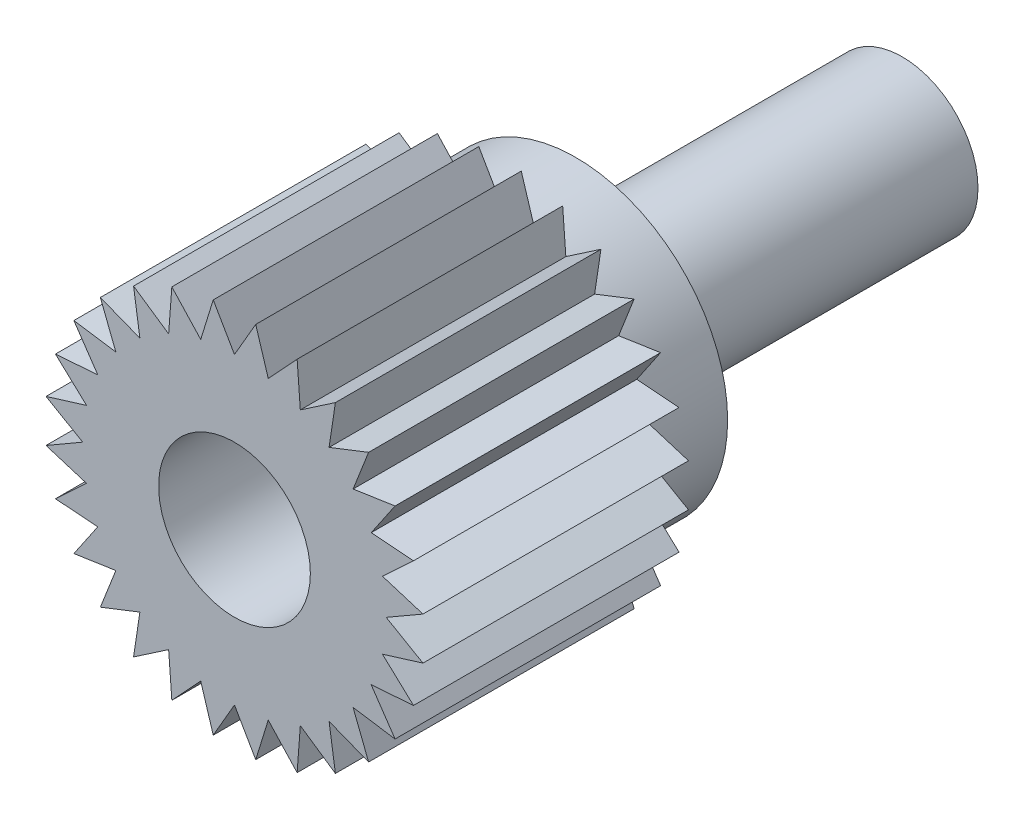
SolidWorks part; units mm, degrees
ref_plane "前视基准面" through (0, 0, 0) normal (0, 0, 1) x (1, 0, 0)
ref_plane "上视基准面" through (0, 0, 0) normal (0, 1, 0) x (1, 0, 0)
ref_plane "右视基准面" through (0, 0, 0) normal (1, 0, 0) x (0, 0, -1)
sketch "草图1" plane through (0, 0, 0) normal (0, 0, 1) x (1, 0, 0)
  circle A0 centre (0, 0) radius 1
extrude "凸台-拉伸1" add sketch "草图1" against normal blind 4.3
sketch "草图2" plane through (0, 0, 0) normal (0, 0, 1) x (1, 0, 0)
  circle A0 centre (0, 0) radius 2
extrude "凸台-拉伸2" add sketch "草图2" along normal blind 1
sketch "草图3" plane through (0, 0, 1) normal (0, 0, 1) x (1, 0, 0)
  line L0 (2.3597, -0.8257) -> (1.8019, -0.8678)
  line L29 (2.4843, -0.2799) -> (1.9499, -0.445)
  line L30 (2.4843, -0.2799) -> (2, 0)
  line L31 (2.3597, -0.8257) -> (1.9499, -0.445)
  line L32 (2.1168, -1.3301) -> (1.5637, -1.247)
  line L33 (2.1168, -1.3301) -> (1.8019, -0.8678)
  line L34 (1.7678, -1.7678) -> (1.247, -1.5637)
  line L35 (1.7678, -1.7678) -> (1.5637, -1.247)
  line L36 (1.3301, -2.1168) -> (0.8678, -1.8019)
  line L37 (1.3301, -2.1168) -> (1.247, -1.5637)
  line L38 (0.8257, -2.3597) -> (0.445, -1.9499)
  line L39 (0.8257, -2.3597) -> (0.8678, -1.8019)
  line L40 (0.2799, -2.4843) -> (0, -2)
  line L41 (0.2799, -2.4843) -> (0.445, -1.9499)
  line L42 (-0.2799, -2.4843) -> (-0.445, -1.9499)
  line L43 (-0.2799, -2.4843) -> (0, -2)
  line L44 (-0.8257, -2.3597) -> (-0.8678, -1.8019)
  line L45 (-0.8257, -2.3597) -> (-0.445, -1.9499)
  line L46 (-1.3301, -2.1168) -> (-1.247, -1.5637)
  line L47 (-1.3301, -2.1168) -> (-0.8678, -1.8019)
  line L48 (-1.7678, -1.7678) -> (-1.5637, -1.247)
  line L49 (-1.7678, -1.7678) -> (-1.247, -1.5637)
  line L50 (-2.1168, -1.3301) -> (-1.8019, -0.8678)
  line L51 (-2.1168, -1.3301) -> (-1.5637, -1.247)
  line L52 (-2.3597, -0.8257) -> (-1.9499, -0.445)
  line L53 (-2.3597, -0.8257) -> (-1.8019, -0.8678)
  line L54 (-2.4843, -0.2799) -> (-2, 0)
  line L55 (-2.4843, -0.2799) -> (-1.9499, -0.445)
  line L56 (-2.4843, 0.2799) -> (-1.9499, 0.445)
  line L57 (-2.4843, 0.2799) -> (-2, 0)
  line L58 (-2.3597, 0.8257) -> (-1.8019, 0.8678)
  line L59 (-2.3597, 0.8257) -> (-1.9499, 0.445)
  line L60 (-2.1168, 1.3301) -> (-1.5637, 1.247)
  line L61 (-2.1168, 1.3301) -> (-1.8019, 0.8678)
  line L62 (-1.7678, 1.7678) -> (-1.247, 1.5637)
  line L63 (-1.7678, 1.7678) -> (-1.5637, 1.247)
  line L64 (-1.3301, 2.1168) -> (-0.8678, 1.8019)
  line L65 (-1.3301, 2.1168) -> (-1.247, 1.5637)
  line L66 (-0.8257, 2.3597) -> (-0.445, 1.9499)
  line L67 (-0.8257, 2.3597) -> (-0.8678, 1.8019)
  line L68 (-0.2799, 2.4843) -> (0, 2)
  line L69 (-0.2799, 2.4843) -> (-0.445, 1.9499)
  line L70 (0.2799, 2.4843) -> (0.445, 1.9499)
  line L71 (0.2799, 2.4843) -> (0, 2)
  line L72 (0.8257, 2.3597) -> (0.8678, 1.8019)
  line L73 (0.8257, 2.3597) -> (0.445, 1.9499)
  line L74 (1.3301, 2.1168) -> (1.247, 1.5637)
  line L75 (1.3301, 2.1168) -> (0.8678, 1.8019)
  line L76 (1.7678, 1.7678) -> (1.5637, 1.247)
  line L77 (1.7678, 1.7678) -> (1.247, 1.5637)
  line L78 (2.1168, 1.3301) -> (1.8019, 0.8678)
  line L79 (2.1168, 1.3301) -> (1.5637, 1.247)
  line L80 (2.3597, 0.8257) -> (1.9499, 0.445)
  line L81 (2.3597, 0.8257) -> (1.8019, 0.8678)
  line L82 (2.4843, 0.2799) -> (2, 0)
  line L83 (2.4843, 0.2799) -> (1.9499, 0.445)
  arc A1 (0.445, -1.9499) -> (0.8678, -1.8019) centre (0, 0) ccw construction
  arc A2 (0, 2) -> (-0.445, 1.9499) centre (0, 0) ccw construction
  arc A3 (-1.5637, -1.247) -> (-1.247, -1.5637) centre (0, 0) ccw construction
  dimension "D1" = 28
extrude "凸台-拉伸3" add sketch "草图3" along normal blind 3.5
ref_point "点1"
sketch "草图4" plane through (0, 0, 4.5) normal (0, 0, 1) x (1, 0, 0)
  circle A0 centre (0, 0) radius 1
extrude "切除-拉伸1" cut sketch "草图4" against normal blind 3 contours A0
